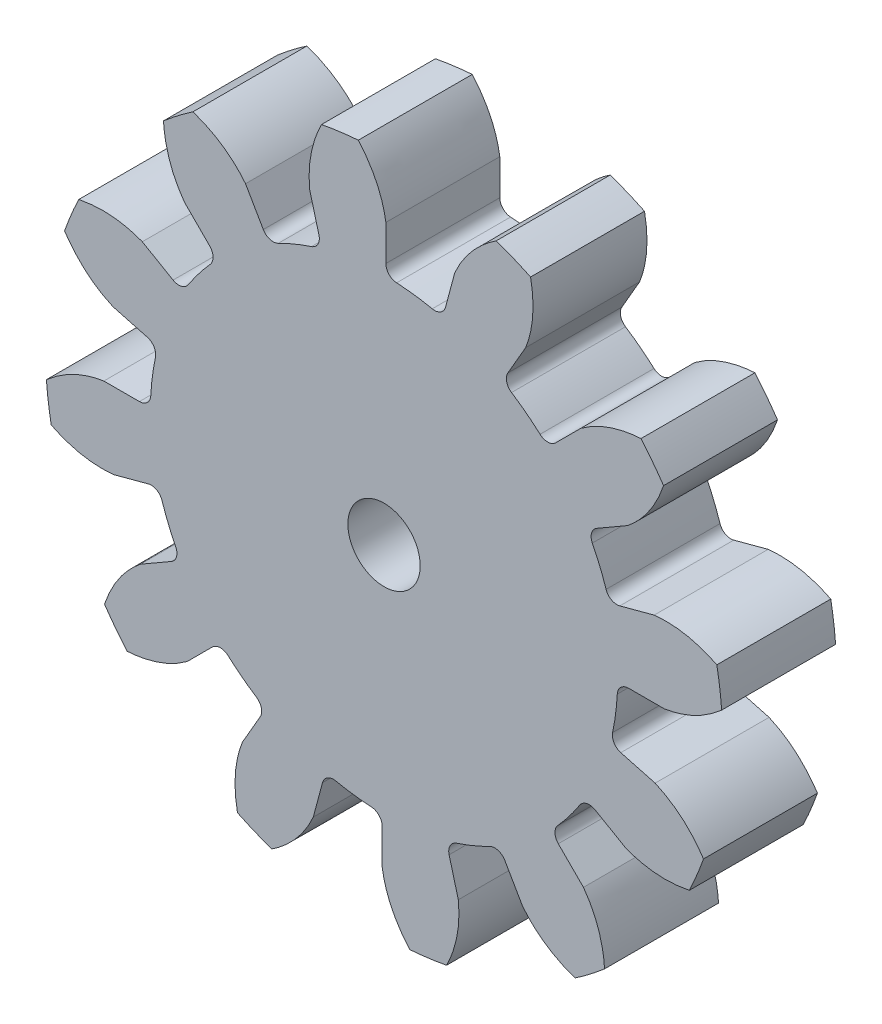
SolidWorks part; units mm, degrees
ref_plane "Front" through (0, 0, 0) normal (0, 0, 1) x (1, 0, 0)
ref_plane "Top" through (0, 0, 0) normal (0, 1, 0) x (1, 0, 0)
ref_plane "Right" through (0, 0, 0) normal (1, 0, 0) x (0, 0, -1)
sketch "Sketch1" plane through (0, 0, 0) normal (0, 0, 1) x (1, 0, 0)
  line L0 (-152.4, 0) -> (152.4, 0) construction
  circle A0 centre (0, 0) radius 14.859
  circle A1 centre (0, 0) radius 12.7 construction
  circle A3 centre (0, 0) radius 10.251 construction
  dimension "D1" = 2.449
  dimension "D2" = 4.608
  dimension "D3" = 2.159
extrude "Boss-Extrude1" add sketch "Sketch1" against normal blind 5
sketch "Sketch3" plane through (0, 0, 0) normal (0, 0, 1) x (1, 0, 0)
  line L0 (0, 0) -> (0, 14.859) construction
  line L1 (-3.0785, 11.9038) -> (0, 12.7)
  line L2 (-9.5921, 12.7) -> (9.5921, 12.7) construction
  line L3 (-9.2865, 10.2983) -> (9.2865, 15.1017) construction
  line L4 (-3.0785, 11.9038) -> (0, 0) construction
  line L5 (-7.8523, 9.4615) -> (0, 0) construction
  line L6 (-7.8523, 9.4615) -> (-1.2457, 14.9445) construction
  line L7 (-2.1466, 12.1066) -> (0, 0) construction
  line L8 (-2.1466, 12.1066) -> (0.045, 12.4952) construction
  arc A0 (-3.0785, 11.9038) -> (-7.8523, 9.4615) centre (0, 0) ccw
  circle A1 centre (0, 0) radius 12.7 construction
  circle A2 centre (0, 0) radius 12.2955 construction
  arc A3 (-3.0785, 11.9038) -> (-2.1466, 12.1066) centre (0, 0) cw
  circle A4 centre (0, 0) radius 14.859 construction
  point P6 (0, 12.7)
  dimension "D1" = 3.1798
  dimension "Pressure Angle" = 14.5
  dimension "D2" = 5.4057
  dimension "D3" = 8.5855
  dimension "D4" = 0.9539
  dimension "D5" = 2.2259
sketch "Sketch4" plane through (0, 0, 0) normal (0, 0, 1) x (1, 0, 0)
  line L0 (0, 0) -> (1.6435, 12.4836) construction
  line L1 (0.0801, 12.2952) -> (0.0801, 10.2507)
  line L2 (0, 12.7) -> (3.287, 12.2673) construction
  line L3 (3.1048, 11.897) -> (2.5757, 9.9222)
  line L4 (0.0801, 10.2507) -> (0, 0) construction
  line L5 (0, 0) -> (0, 14.859) construction
  line L6 (-7.8523, 9.4615) -> (-1.2457, 14.9445) construction
  line L7 (-7.8523, 9.4615) -> (-1.2457, 14.9445) construction
  arc A0 (2.5757, 9.9222) -> (0.0801, 10.2507) centre (0, 0) ccw
  arc A1 (0, 12.7) -> (3.287, 12.2673) centre (0, 0) cw construction
  circle A2 centre (0, 0) radius 12.7 construction
  circle A3 centre (0, 0) radius 12.2955 construction
  circle A4 centre (0, 0) radius 10.251 construction
  arc A5 (5.0712, 14.1129) -> (-1.2457, 14.9445) centre (0, 0) ccw
  spline S0 degree 2 poles (-1.2457, 14.9445) (-0.1467, 13.7689) (0.0801, 12.2952) knots 0 0 0 1 1 1
  spline S1 degree 2 poles (5.0712, 14.1129) (3.7054, 13.2617) (3.1048, 11.897) knots 0 0 0 1 1 1
  dimension "D1" = 3.3249
extrude "Cut-Extrude1" cut sketch "Sketch4" against normal through all
fillet "Fillet1" radius 0.4987 2 edges at (2.5757, 9.9222, -2.5) (0.0801, 10.2507, -2.5)
pattern_circular "CirPattern1" count 12 over 360 about axis through (0, 0, -5) along (0, 0, 1) of "Cut-Extrude1", "Fillet1"
sketch "Sketch5" plane through (0, 0, 0) normal (0, 0, 1) x (1, 0, 0)
  circle A0 centre (0, 0) radius 1.5875
  circle A1 centre (0, 0) radius 6.35 construction
  dimension "Bore Min" = 3.175
  dimension "Bore Max" = 12.7
extrude "Cut-Extrude2" cut sketch "Sketch5" against normal through all
sketch "Pitch Dia" plane through (0, 0, 0) normal (0, 0, 1) x (1, 0, 0)
  circle A0 centre (0, 0) radius 12.7 construction
  circle A1 centre (0, 0) radius 12.7
equation "\"D1@Sketch4\" = 1.5708/(\"Number of Teeth@Sketch1\"/\"Ptich Dia@Sketch1\")"
equation "\"D1@CirPattern1\" = \"Number of Teeth@Sketch1\""
equation "\"D1@Fillet1\" = \"D1@Sketch4\"*.15"
equation "\"D1@Sketch1\" = 1.157/(\"Number of Teeth@Sketch1\"/\"Ptich Dia@Sketch1\")"
